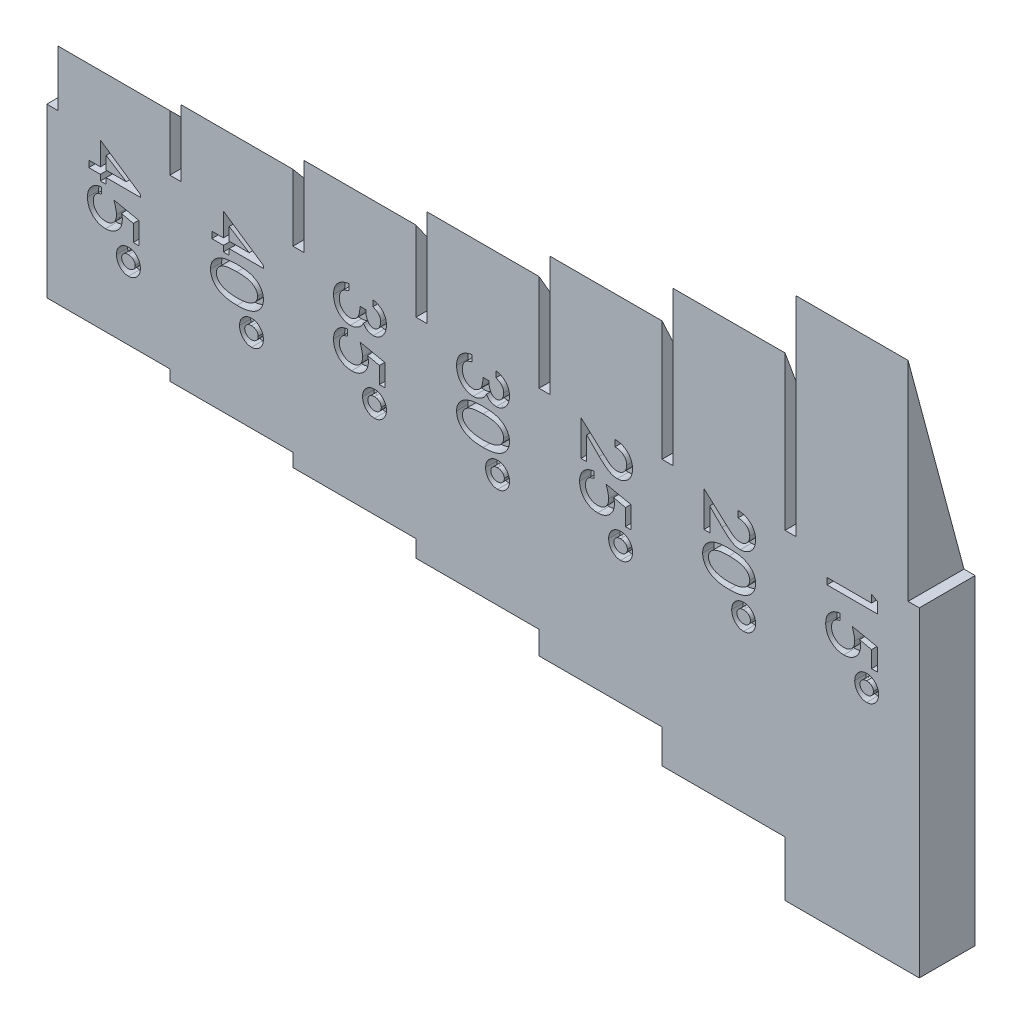
SolidWorks part; units mm, degrees
ref_plane "Front" through (0, 0, 0) normal (0, 0, 1) x (1, 0, 0)
ref_plane "Top" through (0, 0, 0) normal (0, 1, 0) x (1, 0, 0)
ref_plane "Right" through (0, 0, 0) normal (1, 0, 0) x (0, 0, -1)
sketch "Sketch1" plane through (0, 0, 0) normal (1, 0, 0) x (0, -1, 0)
  line L0 (5, 5) -> (10, 0)
  line L1 (-5, 5) -> (5, 5)
  line L2 (-5, 5) -> (-5, 0)
  line L3 (-5, 0) -> (5, 0)
  line L4 (5, 5) -> (5, 0)
  line L5 (10, 0) -> (5, 0)
  line L6 (-5, 5) -> (-10, 0)
  line L7 (-10, 0) -> (-5, 0)
  dimension "D1" = 10
  dimension "D2" = 5
  dimension "D3" = 45
  dimension "D4" = 45
extrude "Boss-Extrude1" add sketch "Sketch1" along normal blind 10
sketch "Sketch2" plane through (0, 0, 0) normal (-1, 0, 0) x (0, 1, 0)
  line L2 (5, 5) -> (-10, 5)
  line L3 (5, 5) -> (5, 0)
  line L4 (5, 0) -> (-10, 0)
  line L6 (-10, 5) -> (-10, 0)
extrude "Boss-Extrude3" add sketch "Sketch2" along normal blind 1
sketch "Sketch3" plane through (10, 0, 0) normal (1, 0, 0) x (0, 0, -1)
  line L0 (5, -5) -> (0, -10.9588)
  line L1 (5, 5) -> (0, 5)
  line L2 (5, 5) -> (5, -10.9588)
  line L3 (5, -10.9588) -> (0, -10.9588)
  line L4 (0, 5) -> (0, -10.9588)
  line L6 (0, 10) -> (0, -10) construction
  line M1 (0, 10) -> (0, -10)
  line M2 (0, -10) -> (5, -5)
  line M3 (5, -5) -> (5, 5)
  dimension "D1" = 40
extrude "Boss-Extrude4" add sketch "Sketch3" along normal blind 1 contours L1 M3 M1 M2 | L3 L2 L0 | L4 L0 M2
sketch "Sketch4" plane through (11, 0, 0) normal (1, 0, 0) x (0, 0, -1)
  line L0 (0, -10.9588) -> (5, -5)
  line L2 (5, -10.9588) -> (5, 5) construction
  line L4 (5, -5) -> (5, 5)
  line L5 (5, 5) -> (0, 10.9588)
  line L6 (0, 10.9588) -> (0, -10.9588)
  dimension "D1" = 40
  dimension "D2" = 10
extrude "Boss-Extrude5" add sketch "Sketch4" along normal blind 10
sketch "Sketch5" plane through (21, 0, 0) normal (1, 0, 0) x (0, 0, -1)
  line L0 (0, -12.1407) -> (5, -5)
  line L1 (5, 5) -> (0, 5)
  line L2 (5, 5) -> (5, -12.1407)
  line L3 (5, -12.1407) -> (0, -12.1407)
  line L4 (0, 5) -> (0, -12.1407)
  line L5 (0, 10.9588) -> (0, -10.9588) construction
  line M1 (0, 10.9588) -> (0, -10.9588)
  line M2 (0, -10.9588) -> (5, -5)
  line M3 (5, -5) -> (5, 5)
  dimension "D1" = 35
extrude "Boss-Extrude6" add sketch "Sketch5" along normal blind 1 contours L3 L2 L0 | L4 L0 M2 | L1 M3 M1 M2
sketch "Sketch6" plane through (22, 0, 0) normal (1, 0, 0) x (0, 0, -1)
  line L0 (5, 5) -> (0, 12.1407)
  line L1 (0, 12.1407) -> (0, -12.1407)
  line L2 (0, -12.1407) -> (5, -5)
  line L3 (5, 5) -> (5, -12.1407) construction
  line L4 (5, -5) -> (5, 5)
  dimension "D1" = 10
  dimension "D2" = 35
extrude "Boss-Extrude7" add sketch "Sketch6" along normal blind 10
sketch "Sketch7" plane through (32, 0, 0) normal (1, 0, 0) x (0, 0, -1)
  line L0 (0, -13.6603) -> (5, -5)
  line L1 (5, 5) -> (0, 5)
  line L2 (5, 5) -> (5, -13.6603)
  line L3 (5, -13.6603) -> (0, -13.6603)
  line L4 (0, 5) -> (0, -13.6603)
  line L5 (0, 12.1407) -> (0, -12.1407) construction
  line M1 (5, -5) -> (5, 5)
  line M3 (0, 12.1407) -> (0, -12.1407)
  line M4 (0, -12.1407) -> (5, -5)
  dimension "D1" = 30
extrude "Boss-Extrude8" add sketch "Sketch7" along normal blind 1 contours L3 L2 L0 | L4 L0 M4 | L1 M1 M3 M4
sketch "Sketch8" plane through (33, 0, 0) normal (1, 0, 0) x (0, 0, -1)
  line L0 (5, 5) -> (0, 13.6603)
  line L1 (0, 13.6603) -> (0, -13.6603)
  line L2 (0, -13.6603) -> (5, -5)
  line L3 (5, 5) -> (5, -13.6603) construction
  line L4 (5, -5) -> (5, 5)
  dimension "D1" = 10
  dimension "D2" = 30
extrude "Boss-Extrude9" add sketch "Sketch8" along normal blind 10
sketch "Sketch9" plane through (43, 0, 0) normal (1, 0, 0) x (0, 0, -1)
  line L0 (0, 13.6603) -> (0, -13.6603) construction
  line L1 (5, 5) -> (0, 5)
  line L2 (5, 5) -> (5, -15.7225)
  line L3 (5, -15.7225) -> (0, -15.7225)
  line L4 (0, 5) -> (0, -15.7225)
  line L5 (0, -15.7225) -> (5, -5)
  line M1 (5, -5) -> (5, 5)
  line M3 (0, 13.6603) -> (0, -13.6603)
  line M4 (0, -13.6603) -> (5, -5)
  dimension "D1" = 25
extrude "Boss-Extrude10" add sketch "Sketch9" along normal blind 1 contours L5 L3 L2 | L4 L5 M4 | L1 M1 M3 M4
sketch "Sketch10" plane through (44, 0, 0) normal (1, 0, 0) x (0, 0, -1)
  line L0 (5, 5) -> (0, 15.7225)
  line L1 (0, 15.7225) -> (0, -15.7225)
  line L2 (0, -15.7225) -> (5, -5)
  line L3 (5, 5) -> (5, -15.7225) construction
  line L4 (5, -5) -> (5, 5)
  dimension "D1" = 10
  dimension "D2" = 25
extrude "Boss-Extrude11" add sketch "Sketch10" along normal blind 10
sketch "Sketch11" plane through (54, 0, 0) normal (1, 0, 0) x (0, 0, -1)
  line L0 (0, 15.7225) -> (0, -15.7225) construction
  line L1 (5, 5) -> (0, 5)
  line L2 (5, 5) -> (5, -18.7374)
  line L3 (5, -18.7374) -> (0, -18.7374)
  line L4 (0, 5) -> (0, -18.7374)
  line L5 (0, -18.7374) -> (5, -5)
  line M1 (5, -5) -> (5, 5)
  line M3 (0, 15.7225) -> (0, -15.7225)
  line M4 (0, -15.7225) -> (5, -5)
  dimension "D1" = 20
extrude "Boss-Extrude12" add sketch "Sketch11" along normal blind 1 contours L5 L3 L2 | L4 L5 M4 | L1 M1 M3 M4
sketch "Sketch12" plane through (55, 0, 0) normal (1, 0, 0) x (0, 0, -1)
  line L0 (5, 5) -> (0, 18.7374)
  line L1 (0, 18.7374) -> (0, -18.7374)
  line L2 (0, -18.7374) -> (5, -5)
  line L3 (5, 5) -> (5, -18.7374) construction
  line L4 (5, -5) -> (5, 5)
  dimension "D1" = 20
  dimension "D2" = 10
extrude "Boss-Extrude13" add sketch "Sketch12" along normal blind 10
sketch "Sketch13" plane through (65, 0, 0) normal (1, 0, 0) x (0, 0, -1)
  line L0 (0, -23.6603) -> (5, -5)
  line L1 (5, 5) -> (0, 5)
  line L2 (5, 5) -> (5, -23.6603)
  line L3 (5, -23.6603) -> (0, -23.6603)
  line L4 (0, 5) -> (0, -23.6603)
  line L5 (0, 18.7374) -> (0, -18.7374) construction
  line M1 (5, -5) -> (5, 5)
  line M3 (0, 18.7374) -> (0, -18.7374)
  line M4 (0, -18.7374) -> (5, -5)
  dimension "D1" = 15
extrude "Boss-Extrude14" add sketch "Sketch13" along normal blind 1 contours L3 L2 L0 | L4 L0 M4 | L1 M1 M3 M4
sketch "Sketch14" plane through (66, 0, 0) normal (1, 0, 0) x (0, 0, -1)
  line L0 (5, 5) -> (0, 23.6603)
  line L1 (0, 23.6603) -> (0, -23.6603)
  line L2 (0, -23.6603) -> (5, -5)
  line L3 (5, 5) -> (5, -23.6603) construction
  line L4 (5, -5) -> (5, 5)
  dimension "D1" = 10
  dimension "D2" = 15
extrude "Boss-Extrude15" add sketch "Sketch14" along normal blind 10
sketch "Sketch15" plane through (76, 0, 0) normal (1, 0, 0) x (0, 0, -1)
  line L1 (5, 5) -> (0, 5)
  line L2 (5, 5) -> (5, -23.6603)
  line L3 (5, -23.6603) -> (0, -23.6603)
  line L4 (0, 5) -> (0, -23.6603)
extrude "Boss-Extrude16" add sketch "Sketch15" along normal blind 1
sketch "Sketch16" plane through (0, 0, 0) normal (0, 0, 1) x (1, 0, 0)
  line L0 (68.75, 5) -> (68.75, -5) construction
  line L1 (66, 5) -> (65, 5) construction
  line L2 (66, 23.6603) -> (66, 5) construction
  line L3 (57.75, 5) -> (57.75, -5) construction
  line L4 (46.75, 5) -> (46.75, -5) construction
  line L5 (35.75, 5) -> (35.75, -5) construction
  line L6 (24.75, 5) -> (24.75, -5) construction
  line L7 (13.75, 5) -> (13.75, -5) construction
  line L8 (2.75, 5) -> (2.75, -5) construction
  text T0 "15°" font "Century Gothic" height 4.5
  text T1 "20°" font "Century Gothic" height 4.5
  text T2 "25°" font "Century Gothic" height 4.5
  text T3 "30°" font "Century Gothic" height 4.5
  text T4 "35°" font "Century Gothic" height 4.5
  text T5 "40°" font "Century Gothic" height 4.5
  text T6 "45°" font "Century Gothic" height 4.5
  dimension "D1" = 10
  dimension "D2" = 2.75
  dimension "D3" = 7
extrude "Cut-Extrude1" cut sketch "Sketch16" against normal blind 1
